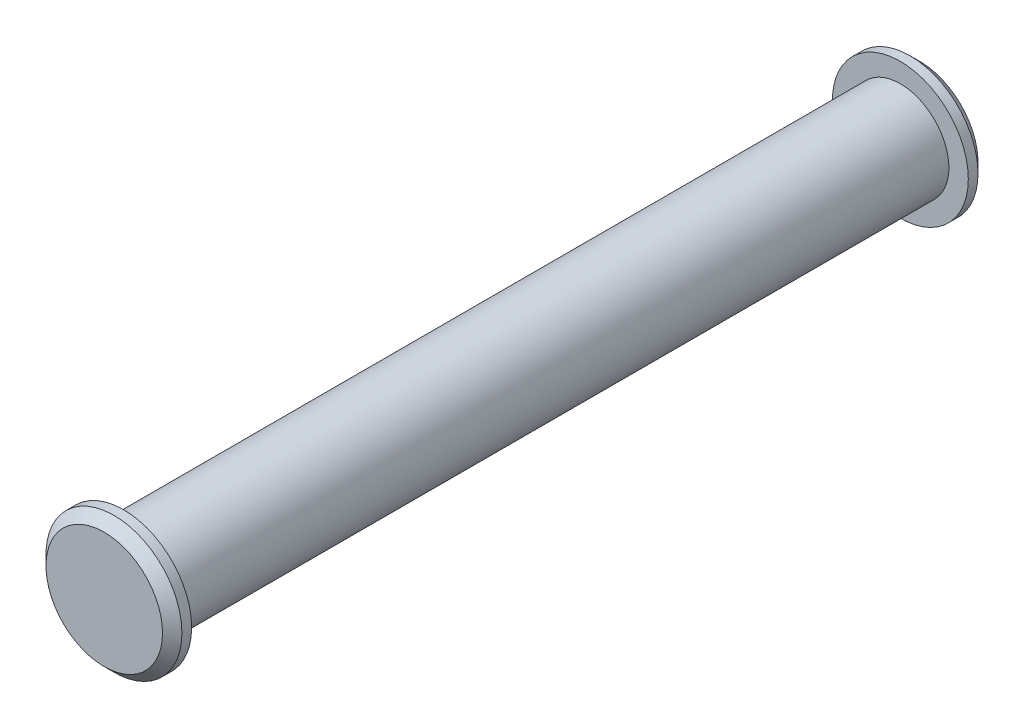
SolidWorks part; units mm, degrees
ref_plane "Front Plane" through (0, 0, 0) normal (0, 0, 1) x (1, 0, 0)
ref_plane "Top Plane" through (0, 0, 0) normal (0, 1, 0) x (1, 0, 0)
ref_plane "Right Plane" through (0, 0, 0) normal (1, 0, 0) x (0, 0, -1)
sketch "Sketch1" plane through (0, 0, 0) normal (0, 0, 1) x (1, 0, 0)
  circle A0 centre (0, 0) radius 2.5
  dimension "D1" = 5
extrude "Boss-Extrude1" add sketch "Sketch1" along normal mid plane 40
sketch "Sketch2" plane through (0, 0, 20) normal (0, 0, 1) x (1, 0, 0)
  circle A0 centre (0, 0) radius 3.5
  dimension "D1" = 7
extrude "Boss-Extrude2" add sketch "Sketch2" along normal blind 1
mirror "Mirror1" about plane through (0, 0, 0) normal (0, 0, 1) of "Boss-Extrude2"
chamfer "Chamfer1" distance 0.5 angle 45 2 edges at (3.5, 0, -21) (3.5, 0, 21)
